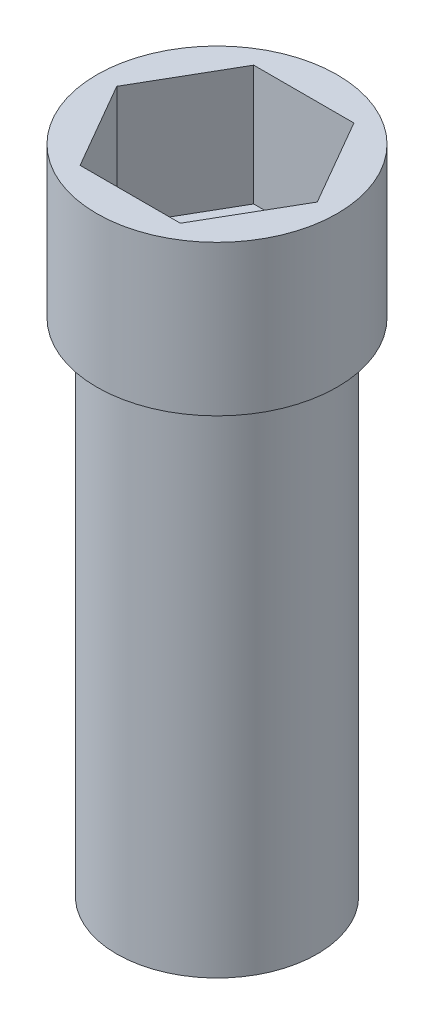
SolidWorks part; units mm, degrees
ref_plane "Front Plane" through (0, 0, 0) normal (0, 0, 1) x (1, 0, 0)
ref_plane "Top Plane" through (0, 0, 0) normal (0, 1, 0) x (1, 0, 0)
ref_plane "Right Plane" through (0, 0, 0) normal (1, 0, 0) x (0, 0, -1)
sketch "Sketch1" plane through (0, 0, 0) normal (0, 1, 0) x (1, 0, 0)
  circle A0 centre (0, 0) radius 254
extrude "Boss-Extrude1" add sketch "Sketch1" against normal blind 1270
sketch "Sketch2" plane through (0, 0, 0) normal (0, 1, 0) x (1, 0, 0)
  circle A0 centre (0, 0) radius 304.8
extrude "Boss-Extrude2" add sketch "Sketch2" along normal blind 381
sketch "Sketch3" plane through (0, 381, 0) normal (0, 1, 0) x (1, 0, 0)
  line L0 (-127.0354, 220.0317) -> (127.0354, 220.0317)
  line L1 (127.0354, 220.0317) -> (254.0708, 0)
  line L2 (254.0708, 0) -> (127.0354, -220.0317)
  line L3 (127.0354, -220.0317) -> (-127.0354, -220.0317)
  line L4 (-127.0354, -220.0317) -> (-254.0708, 0)
  line L5 (-254.0708, 0) -> (-127.0354, 220.0317)
  line L6 (-335.28, 0) -> (335.28, 0) construction
extrude "Cut-Extrude1" cut sketch "Sketch3" against normal blind 304.8
sketch3d "3DSketch1" plane through (0, 0, 0) normal (0, 0, 1) x (1, 0, 0)
  dimension "D1" = 254
sketch "Sketch4" plane through (0, 0, -254) normal (0, 0, 1) x (1, 0, 0)
  line L0 (0, -335.28) -> (0, 335.28) construction
  line L1 (-76.2, -825.5) -> (76.2, -825.5)
  line L2 (-76.2, -825.5) -> (-76.2, -190.5)
  line L3 (-76.2, -190.5) -> (76.2, -190.5)
  line L4 (76.2, -825.5) -> (76.2, -190.5)
  line L5 (-76.2, -825.5) -> (76.2, -190.5) construction
  line L6 (-76.2, -190.5) -> (76.2, -825.5) construction
  line L7 (335.28, 0) -> (-335.28, 0) construction
  point P0 (0, -508)
  dimension "D1" = 635
  dimension "D2" = 152.4
  dimension "D3" = 508
extrude "Cut-Extrude2" cut sketch "Sketch4" along normal blind 101.6
